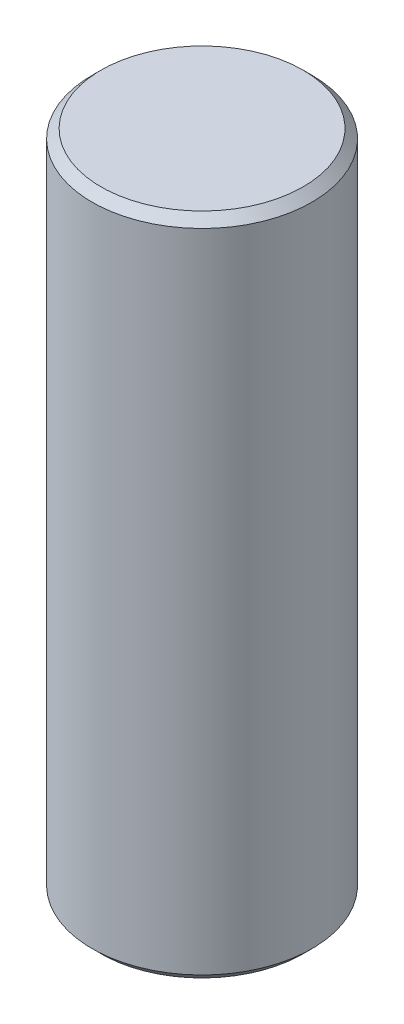
SolidWorks part; units mm, degrees
material "Brass"
ref_plane "Front" through (0, 0, 0) normal (0, 0, 1) x (1, 0, 0)
ref_plane "Top" through (0, 0, 0) normal (0, 1, 0) x (1, 0, 0)
ref_plane "Right" through (0, 0, 0) normal (1, 0, 0) x (0, 0, -1)
sketch "Sketch1" plane through (0, 0, 0) normal (0, 0, 1) x (1, 0, 0)
  line L0 (9.4615, 0.762) -> (9.4615, 56.388)
  line L1 (8.6995, 0) -> (4.7879, 0)
  line L2 (4.7879, 0) -> (4.7879, 2.032)
  line L3 (4.5339, 2.286) -> (0, 2.286)
  line L6 (0, 2.286) -> (0, 57.15)
  line L7 (8.6995, 57.15) -> (0, 57.15)
  line L8 (0, 0) -> (4.7879, 0) construction
  line L9 (0, 0) -> (0, 2.286) construction
  line L10 (4.7879, 2.032) -> (4.5339, 2.286)
  line L12 (9.4615, 56.388) -> (8.6995, 57.15)
  line L13 (9.4615, 0.762) -> (8.6995, 0)
  point P0 (9.4615, 0)
  point P1 (9.4615, 57.15)
  point P4 (4.7879, 2.286)
  dimension "D1" = 57.15
  dimension "D2" = 2.286
  dimension "D5" = 9.5758
  dimension "D6" = 18.923
  dimension "D9" = 0.254
  dimension "D11" = 0.762
  dimension "D12" = 0.762
revolve "Revolve1" add sketch "Sketch1" angle 360 about L9
